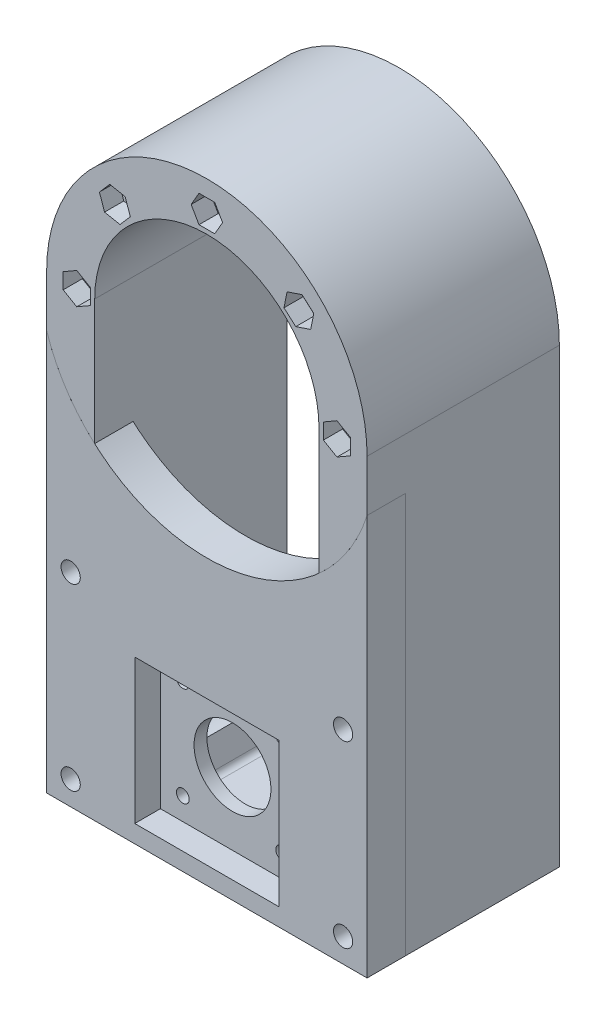
SolidWorks part; units mm, degrees
ref_plane "Alzado" through (0, 0, 0) normal (0, 0, 1) x (1, 0, 0)
ref_plane "Planta" through (0, 0, 0) normal (0, 1, 0) x (1, 0, 0)
ref_plane "Vista lateral" through (0, 0, 0) normal (1, 0, 0) x (0, 0, -1)
sketch "Croquis1" plane through (0, 0, 0) normal (0, 0, 1) x (1, 0, 0)
  line L0 (-35, 0) -> (-35, -116)
  line L1 (-25, -126) -> (25, -126)
  line L2 (35, 0) -> (35, -116)
  line L3 (-50, 0) -> (-50, -141)
  line L4 (-50, -141) -> (50, -141)
  line L5 (50, 0) -> (50, -141)
  line L6 (35, 0) -> (35, -126) construction
  line L7 (-35, -126) -> (35, -126) construction
  line L8 (-35, 0) -> (-35, -126) construction
  arc A0 (35, 0) -> (-35, 0) centre (0, 0) ccw
  arc A1 (50, 0) -> (-50, 0) centre (0, 0) ccw
  arc A2 (35, -116) -> (25, -126) centre (25, -116) cw
  arc A3 (-35, -116) -> (-25, -126) centre (-25, -116) ccw
  dimension "D1" = 141
  dimension "D2" = 15
  dimension "D3" = 10
extrude "Saliente-Extruir1" add sketch "Croquis1" along normal blind 60
sketch "Croquis2" plane through (0, 0, 60) normal (0, 0, 1) x (1, 0, 0)
  circle A0 centre (0, 0) radius 40.605
  circle A1 centre (0, 40.605) radius 3
  circle A2 centre (28.7121, 28.7121) radius 3
  circle A3 centre (40.605, 0) radius 3
  circle A4 centre (28.7121, -28.7121) radius 3
  circle A5 centre (0, -40.605) radius 3
  circle A6 centre (-28.7121, -28.7121) radius 3
  circle A7 centre (-40.605, 0) radius 3
  circle A8 centre (-28.7121, 28.7121) radius 3
  point P22 (0, 0)
  dimension "D1" = 81.21
  dimension "D2" = 6
  dimension "D3" = 8
extrude "Cortar-Extruir1" cut sketch "Croquis2" against normal blind 60 contours A8 | A7 | A1 | A2 | A3
sketch "Croquis3" plane through (0, 0, 60) normal (0, 0, 1) x (1, 0, 0)
  line L1 (4.9075, 40.605) -> (2.4537, 44.855)
  line L2 (2.4537, 44.855) -> (-2.4537, 44.855)
  line L3 (-2.4537, 44.855) -> (-4.9075, 40.605)
  line L4 (-4.9075, 40.605) -> (-2.4537, 36.355)
  line L5 (-2.4537, 36.355) -> (2.4537, 36.355)
  line L6 (2.4537, 36.355) -> (4.9075, 40.605)
  line L7 (33.3651, 30.2717) -> (29.688, 33.5215)
  line L8 (29.688, 33.5215) -> (25.0349, 31.9619)
  line L9 (25.0349, 31.9619) -> (24.059, 27.1525)
  line L10 (24.059, 27.1525) -> (27.7362, 23.9026)
  line L11 (27.7362, 23.9026) -> (32.3893, 25.4622)
  line L12 (32.3893, 25.4622) -> (33.3651, 30.2717)
  line L13 (40.605, -4.9075) -> (44.855, -2.4537)
  line L14 (44.855, -2.4537) -> (44.855, 2.4537)
  line L15 (44.855, 2.4537) -> (40.605, 4.9075)
  line L16 (40.605, 4.9075) -> (36.355, 2.4537)
  line L17 (36.355, 2.4537) -> (36.355, -2.4537)
  line L18 (36.355, -2.4537) -> (40.605, -4.9075)
  line L19 (-33.5289, 29.6508) -> (-31.9335, 25.0099)
  line L20 (-31.9335, 25.0099) -> (-27.1166, 24.0712)
  line L21 (-27.1166, 24.0712) -> (-23.8952, 27.7733)
  line L22 (-23.8952, 27.7733) -> (-25.4907, 32.4142)
  line L23 (-25.4907, 32.4142) -> (-30.3075, 33.353)
  line L24 (-30.3075, 33.353) -> (-33.5289, 29.6508)
  line L25 (-40.605, 4.9075) -> (-44.855, 2.4537)
  line L26 (-44.855, 2.4537) -> (-44.855, -2.4537)
  line L27 (-44.855, -2.4537) -> (-40.605, -4.9075)
  line L28 (-40.605, -4.9075) -> (-36.355, -2.4537)
  line L29 (-36.355, -2.4537) -> (-36.355, 2.4537)
  line L30 (-36.355, 2.4537) -> (-40.605, 4.9075)
  circle A0 centre (0, 40.605) radius 4.25 construction
  circle A1 centre (28.7121, 28.7121) radius 4.25 construction
  circle A2 centre (40.605, 0) radius 4.25 construction
  circle A3 centre (-28.7121, 28.7121) radius 4.25 construction
  circle A4 centre (-40.605, 0) radius 4.25 construction
  dimension "D1" = 8.5
  dimension "D2" = 8.5
  dimension "D3" = 8.5
  dimension "D4" = 8.5
  dimension "D5" = 8.5
extrude "Cortar-Extruir2" cut sketch "Croquis3" against normal blind 6
sketch "Croquis4" plane through (0, 0, 60) normal (0, 0, 1) x (1, 0, 0)
  line L0 (-50, -16.0078) -> (-50, -141)
  line L1 (-50, -141) -> (50, -141)
  line L2 (50, -141) -> (50, -16.0078)
  arc A0 (-50, -16.0078) -> (50, -16.0078) centre (0, 0) ccw
  dimension "D1" = 105
extrude "Cortar-Extruir3" cut sketch "Croquis4" against normal blind 12
sketch "Croquis5" plane through (0, 0, 48) normal (0, 0, 1) x (1, 0, 0)
  line L0 (-35, -77.5656) -> (-50, -77.5656) construction
  line L1 (-35, -39.1312) -> (-35, -116) construction
  line L2 (-50, -16.0078) -> (-50, -141) construction
  line L3 (0, -141) -> (0, -126) construction
  line L4 (-50, -141) -> (50, -141) construction
  line L5 (-25, -126) -> (25, -126) construction
  line L6 (0, -133.5) -> (-50, -133.5) construction
  line L7 (-42.5, -77.5656) -> (-42.5, -133.5) construction
  line L8 (42.5, -77.5656) -> (42.5, -133.5) construction
  circle A0 centre (-42.5, -77.5656) radius 3
  circle A1 centre (-42.5, -133.5) radius 3
  circle A2 centre (42.5, -77.5656) radius 3
  circle A3 centre (42.5, -133.5) radius 3
  dimension "D1" = 6
extrude "Cortar-Extruir4" cut sketch "Croquis5" against normal up to surface (48 mm away) up to face at (43.605, 0, 0)
sketch "Croquis6" plane through (0, 0, 48) normal (0, 0, 1) x (1, 0, 0)
  line L1 (-42.4213, -82.4724) -> (-38.2112, -79.9509)
  line L2 (-38.2112, -79.9509) -> (-38.2899, -75.044)
  line L3 (-38.2899, -75.044) -> (-42.5787, -72.6587)
  line L4 (-42.5787, -72.6587) -> (-46.7888, -75.1803)
  line L5 (-46.7888, -75.1803) -> (-46.7101, -80.0872)
  line L6 (-46.7101, -80.0872) -> (-42.4213, -82.4724)
  line L7 (42.5, -82.4731) -> (46.75, -80.0193)
  line L8 (46.75, -80.0193) -> (46.75, -75.1119)
  line L9 (46.75, -75.1119) -> (42.5, -72.6581)
  line L10 (42.5, -72.6581) -> (38.25, -75.1119)
  line L11 (38.25, -75.1119) -> (38.25, -80.0193)
  line L12 (38.25, -80.0193) -> (42.5, -82.4731)
  line L13 (-40.0636, -129.2401) -> (-44.971, -129.26)
  line L14 (-44.971, -129.26) -> (-47.4074, -133.52)
  line L15 (-47.4074, -133.52) -> (-44.9364, -137.7599)
  line L16 (-44.9364, -137.7599) -> (-40.029, -137.74)
  line L17 (-40.029, -137.74) -> (-37.5926, -133.48)
  line L18 (-37.5926, -133.48) -> (-40.0636, -129.2401)
  line L19 (44.896, -129.2172) -> (39.9889, -129.2836)
  line L20 (39.9889, -129.2836) -> (37.593, -133.5664)
  line L21 (37.593, -133.5664) -> (40.104, -137.7828)
  line L22 (40.104, -137.7828) -> (45.0111, -137.7164)
  line L23 (45.0111, -137.7164) -> (47.407, -133.4336)
  line L24 (47.407, -133.4336) -> (44.896, -129.2172)
  circle A0 centre (-42.5, -77.5656) radius 4.25 construction
  circle A1 centre (42.5, -77.5656) radius 4.25 construction
  circle A2 centre (-42.5, -133.5) radius 4.25 construction
  circle A3 centre (42.5, -133.5) radius 4.25 construction
  dimension "D1" = 8.5
extrude "Cortar-Extruir5" cut sketch "Croquis6" against normal blind 6
sketch "Croquis7" plane through (0, 0, 0) normal (0, 0, -1) x (-1, 0, 0)
  line L1 (2.3579, 44.9089) -> (-2.5484, 44.7989)
  line L2 (-2.5484, 44.7989) -> (-4.9062, 40.495)
  line L3 (-4.9062, 40.495) -> (-2.3579, 36.3011)
  line L4 (-2.3579, 36.3011) -> (2.5484, 36.4111)
  line L5 (2.5484, 36.4111) -> (4.9062, 40.715)
  line L6 (4.9062, 40.715) -> (2.3579, 44.9089)
  line L7 (-40.6144, 4.9075) -> (-44.8597, 2.4456)
  line L8 (-44.8597, 2.4456) -> (-44.8503, -2.4619)
  line L9 (-44.8503, -2.4619) -> (-40.5956, -4.9075)
  line L10 (-40.5956, -4.9075) -> (-36.3503, -2.4456)
  line L11 (-36.3503, -2.4456) -> (-36.3597, 2.4619)
  line L12 (-36.3597, 2.4619) -> (-40.6144, 4.9075)
  line L13 (44.8825, -2.4055) -> (44.827, 2.5017)
  line L14 (44.827, 2.5017) -> (40.5495, 4.9072)
  line L15 (40.5495, 4.9072) -> (36.3275, 2.4055)
  line L16 (36.3275, 2.4055) -> (36.383, -2.5017)
  line L17 (36.383, -2.5017) -> (40.6605, -4.9072)
  line L18 (40.6605, -4.9072) -> (44.8825, -2.4055)
  line L19 (-42.1314, -72.672) -> (-46.5537, -74.7995)
  line L20 (-46.5537, -74.7995) -> (-46.9223, -79.6932)
  line L21 (-46.9223, -79.6932) -> (-42.8686, -82.4592)
  line L22 (-42.8686, -82.4592) -> (-38.4463, -80.3316)
  line L23 (-38.4463, -80.3316) -> (-38.0777, -75.438)
  line L24 (-38.0777, -75.438) -> (-42.1314, -72.672)
  line L25 (42.0844, -72.6757) -> (38.0575, -75.4806)
  line L26 (38.0575, -75.4806) -> (38.4731, -80.3705)
  line L27 (38.4731, -80.3705) -> (42.9156, -82.4554)
  line L28 (42.9156, -82.4554) -> (46.9425, -79.6506)
  line L29 (46.9425, -79.6506) -> (46.5269, -74.7607)
  line L30 (46.5269, -74.7607) -> (42.0844, -72.6757)
  line L31 (47.4075, -133.5) -> (44.9537, -129.25)
  line L32 (44.9537, -129.25) -> (40.0463, -129.25)
  line L33 (40.0463, -129.25) -> (37.5925, -133.5)
  line L34 (37.5925, -133.5) -> (40.0463, -137.75)
  line L35 (40.0463, -137.75) -> (44.9537, -137.75)
  line L36 (44.9537, -137.75) -> (47.4075, -133.5)
  line L37 (-44.6369, -137.9178) -> (-39.7425, -137.5595)
  line L38 (-39.7425, -137.5595) -> (-37.6056, -133.1417)
  line L39 (-37.6056, -133.1417) -> (-40.3631, -129.0822)
  line L40 (-40.3631, -129.0822) -> (-45.2575, -129.4405)
  line L41 (-45.2575, -129.4405) -> (-47.3944, -133.8583)
  line L42 (-47.3944, -133.8583) -> (-44.6369, -137.9178)
  circle A0 centre (0, 40.605) radius 4.25 construction
  circle A1 centre (-40.605, 0) radius 4.25 construction
  circle A2 centre (40.605, 0) radius 4.25 construction
  circle A3 centre (-42.5, -77.5656) radius 4.25 construction
  circle A4 centre (42.5, -77.5656) radius 4.25 construction
  circle A5 centre (42.5, -133.5) radius 4.25 construction
  circle A6 centre (-42.5, -133.5) radius 4.25 construction
  dimension "D1" = 8.5
  dimension "D2" = 8.5
extrude "Cortar-Extruir6" cut sketch "Croquis7" against normal blind 6
sketch "Croquis8" plane through (0, 0, 48) normal (0, 0, 1) x (1, 0, 0)
  line L0 (0, -141) -> (0, -113) construction
  line L2 (-50, -141) -> (50, -141) construction
  line L3 (0, 0) -> (0, -113) construction
  line L4 (-22.8924, -134.009) -> (-25, -126)
  line L13 (-20.9582, -135.5) -> (20.9582, -135.5)
  line L17 (-25, -126) -> (25, -126)
  line L18 (25, -126) -> (22.8924, -134.009)
  arc A0 (22.8924, -134.009) -> (20.9582, -135.5) centre (20.9582, -133.5) cw
  arc A1 (-22.8924, -134.009) -> (-20.9582, -135.5) centre (-20.9582, -133.5) ccw
  dimension "D2" = 2
  dimension "D1" = 28
extrude "Cortar-Extruir7" cut sketch "Croquis8" against normal up to surface (48 mm away) up to face at (42.5, -133.5, 0)
sketch "Croquis9" plane through (0, 0, 48) normal (0, 0, 1) x (1, 0, 0)
  line L8 (-22.8924, -134.009) -> (-25, -126)
  line L9 (-35, -116) -> (-35, -39.1312)
  line L10 (-50, -16.0078) -> (-50, -141)
  line L11 (-50, -141) -> (50, -141)
  line L12 (50, -141) -> (50, -16.0078)
  line L13 (35, -39.1312) -> (35, -116)
  line L14 (25, -126) -> (22.8924, -134.009)
  line L15 (20.9582, -135.5) -> (-20.9582, -135.5)
  line L18 (-50, -16.0078) -> (-50, -141)
  line L19 (-50, -141) -> (50, -141)
  line L20 (50, -141) -> (50, -16.0078)
  circle A0 centre (-42.5, -77.5656) radius 3
  circle A1 centre (42.5, -77.5656) radius 3
  circle A2 centre (42.5, -133.5) radius 3
  circle A3 centre (-42.5, -133.5) radius 3
  arc A4 (-50, -16.0078) -> (50, -16.0078) centre (0, 0) ccw
  arc A6 (-35, -116) -> (-25, -126) centre (-25, -116) ccw
  arc A7 (-50, -16.0078) -> (-35, -39.1312) centre (0, 0) ccw
  arc A8 (35, -39.1312) -> (50, -16.0078) centre (0, 0) ccw
  arc A9 (25, -126) -> (35, -116) centre (25, -116) ccw
  arc A10 (20.9582, -135.5) -> (22.8924, -134.009) centre (20.9582, -133.5) ccw
  arc A11 (-22.8924, -134.009) -> (-20.9582, -135.5) centre (-20.9582, -133.5) ccw
  arc A13 (-50, -16.0078) -> (-35, -39.1312) centre (0, 0) ccw
  arc A14 (35, -39.1312) -> (50, -16.0078) centre (0, 0) ccw
  line M15 (-22.8924, -134.009) -> (-25, -126)
  arc M16 (-25, -126) -> (-35, -116) centre (-25, -116) cw
  line M17 (-35, -116) -> (-35, -39.1312)
  arc M18 (-35, -39.1312) -> (-50, -16.0078) centre (0, 0) cw
  line M19 (-50, -16.0078) -> (-50, -141)
  line M20 (-50, -141) -> (50, -141)
  line M21 (50, -141) -> (50, -16.0078)
  arc M22 (50, -16.0078) -> (35, -39.1312) centre (0, 0) cw
  line M23 (35, -39.1312) -> (35, -116)
  arc M24 (35, -116) -> (25, -126) centre (25, -116) cw
  line M25 (25, -126) -> (22.8924, -134.009)
  arc M26 (22.8924, -134.009) -> (20.9582, -135.5) centre (20.9582, -133.5) cw
  line M27 (20.9582, -135.5) -> (-20.9582, -135.5)
  arc M28 (-20.9582, -135.5) -> (-22.8924, -134.009) centre (-20.9582, -133.5) cw
  line M29 (44.896, -129.2172) -> (47.407, -133.4336)
  line M30 (47.407, -133.4336) -> (45.0111, -137.7164)
  line M31 (45.0111, -137.7164) -> (40.104, -137.7828)
  line M32 (40.104, -137.7828) -> (37.593, -133.5664)
  line M33 (37.593, -133.5664) -> (39.9889, -129.2836)
  line M34 (39.9889, -129.2836) -> (44.896, -129.2172)
  line M35 (-40.0636, -129.2401) -> (-37.5926, -133.48)
  line M36 (-37.5926, -133.48) -> (-40.029, -137.74)
  line M37 (-40.029, -137.74) -> (-44.9364, -137.7599)
  line M38 (-44.9364, -137.7599) -> (-47.4074, -133.52)
  line M39 (-47.4074, -133.52) -> (-44.971, -129.26)
  line M40 (-44.971, -129.26) -> (-40.0636, -129.2401)
  line M41 (42.5, -82.4731) -> (38.25, -80.0193)
  line M42 (38.25, -80.0193) -> (38.25, -75.1119)
  line M43 (38.25, -75.1119) -> (42.5, -72.6581)
  line M44 (42.5, -72.6581) -> (46.75, -75.1119)
  line M45 (46.75, -75.1119) -> (46.75, -80.0193)
  line M46 (46.75, -80.0193) -> (42.5, -82.4731)
  line M47 (-42.4213, -82.4724) -> (-46.7101, -80.0872)
  line M48 (-46.7101, -80.0872) -> (-46.7888, -75.1803)
  line M49 (-46.7888, -75.1803) -> (-42.5787, -72.6587)
  line M50 (-42.5787, -72.6587) -> (-38.2899, -75.044)
  line M51 (-38.2899, -75.044) -> (-38.2112, -79.9509)
  line M52 (-38.2112, -79.9509) -> (-42.4213, -82.4724)
  dimension "D1" = 0
extrude "Saliente-Extruir2" add sketch "Croquis9" along normal up to surface (12 mm away) separate body contours M28 M15 M16 M17 M18 M19 M20 M21 M22 M23 M24 M25 M26 M27 M34 M29 M30 M31 M32 M33 M46 M41 M42 M43 M44 M45 M52 M47 M48 M49 M50 M51 M40 M35 M36 M37 M38 M39 | A0 M47 M52 M51 M50 M49 M48 | A3 M35 M40 M39 M38 M37 M36 | A2 M29 M34 M33 M32 M31 M30 | A1 M41 M46 M45 M44 M43 M42 | A4 M17 M16 M15 M28 M27 M26 M25 M24 M23 up to face at (0, -3.4102, 60)
sketch "Croquis10" plane through (0, 0, 60) normal (0, 0, 1) x (1, 0, 0)
  line L0 (0, -141) -> (0, -113) construction
  line L2 (-50, -141) -> (50, -141) construction
  circle A0 centre (0, -113) radius 12
  dimension "D1" = 24
extrude "Cortar-Extruir8" cut sketch "Croquis10" against normal up to surface (12 mm away) up to face at (0, -87.627, 48)
sketch "Croquis11" plane through (0, 0, 60) normal (0, 0, 1) x (1, 0, 0)
  line L1 (-22.5, -135.5) -> (22.5, -135.5)
  line L2 (-22.5, -135.5) -> (-22.5, -90.5)
  line L3 (-22.5, -90.5) -> (22.5, -90.5)
  line L4 (22.5, -135.5) -> (22.5, -90.5)
  line L5 (-22.5, -135.5) -> (22.5, -90.5) construction
  line L6 (-22.5, -90.5) -> (22.5, -135.5) construction
  point P0 (0, -113)
  dimension "D1" = 45
  dimension "D2" = 45
extrude "Cortar-Extruir9" cut sketch "Croquis11" against normal blind 8
sketch "Croquis12" plane through (0, 0, 52) normal (0, 0, 1) x (1, 0, 0)
  circle A0 centre (-15.5, -97.5) radius 2
  circle A1 centre (15.5, -97.5) radius 2
  circle A2 centre (15.5, -128.5) radius 2
  circle A3 centre (-15.5, -128.5) radius 2
  dimension "D3" = 4
  dimension "D1" = 31
  dimension "D2" = 31
extrude "Cortar-Extruir10" cut sketch "Croquis12" against normal through all
